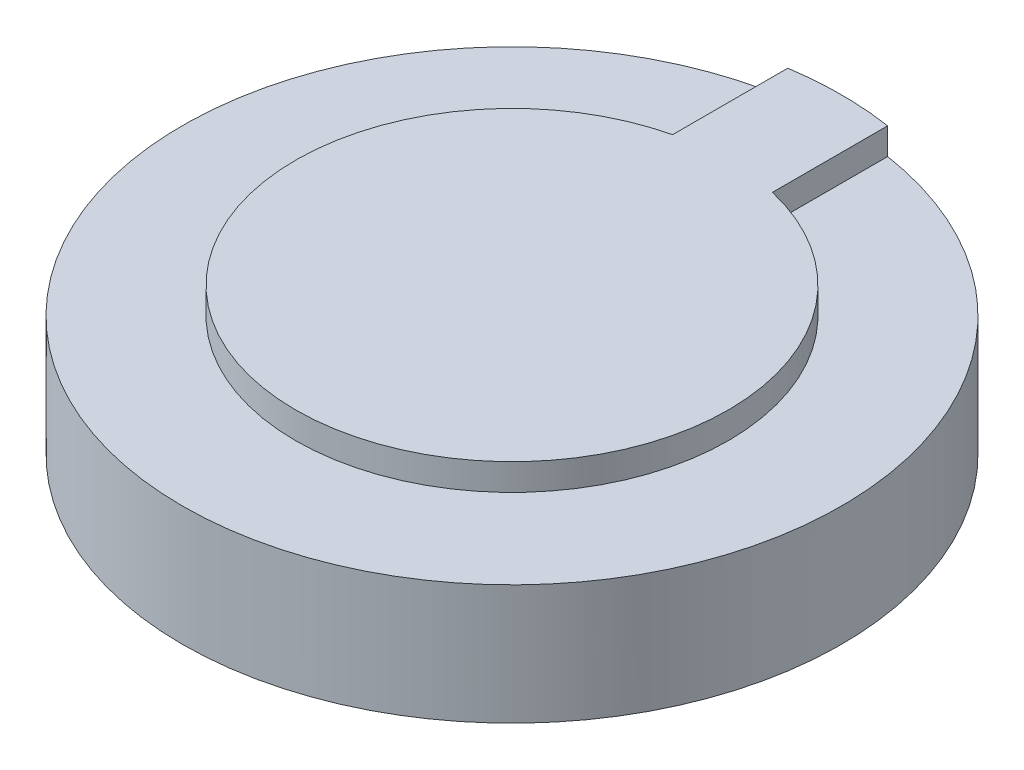
SolidWorks part; units mm, degrees
ref_plane "Front plane" through (0, 0, 0) normal (0, 0, 1) x (1, 0, 0)
ref_plane "Top plane" through (0, 0, 0) normal (0, 1, 0) x (1, 0, 0)
ref_plane "Right Plane" through (0, 0, 0) normal (1, 0, 0) x (0, 0, -1)
sketch "Sketch1" plane through (0, 0, 0) normal (1, 0, 0) x (0, 0, -1)
  line L0 (0, 0) -> (9.9, 0)
  line L1 (9.9, 0) -> (9.9, 3.6)
  line L2 (9.9, 3.6) -> (6.5, 3.6)
  line L3 (6.5, 3.6) -> (6.5, 4.4)
  line L4 (6.5, 4.4) -> (0, 4.4)
  line L5 (0, 4.4) -> (0, 0)
  dimension "D1" = 9.9
  dimension "D2" = 3.6
  dimension "D3" = 4.4
  dimension "D4" = 6.5
revolve "Revolve1" add sketch "Sketch1" angle 360 about L5
sketch "Sketch2" plane through (0, 3.6, 0) normal (0, 1, 0) x (1, 0, 0)
  line L1 (-1.5, 6.3246) -> (1.5, 6.3246)
  line L2 (-1.5, 6.3246) -> (-1.5, 9.7857)
  line L4 (1.5, 6.3246) -> (1.5, 9.7857)
  circle A0 centre (0, 0) radius 6.5 construction
  circle A1 centre (0, 0) radius 6.5 construction
  circle A2 centre (0, 0) radius 9.9 construction
  arc A3 (1.5, 9.7857) -> (-1.5, 9.7857) centre (0, 0) ccw
  dimension "D1" = 3
extrude "Boss-Extrude1" add sketch "Sketch2" along normal blind 0.8
